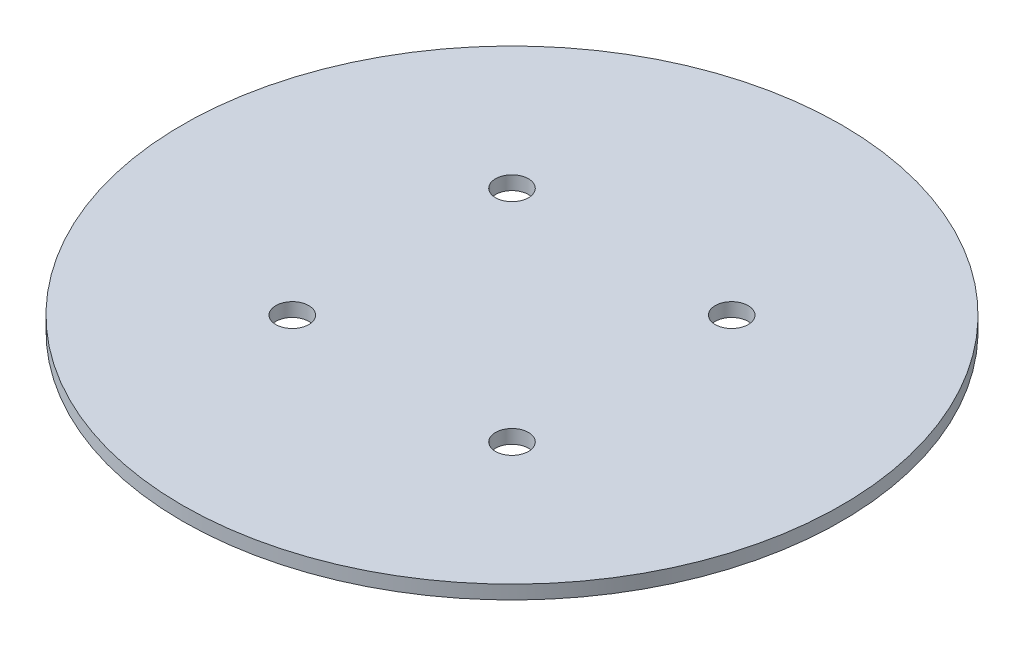
SolidWorks part; units mm, degrees
ref_plane "Front Plane" through (0, 0, 0) normal (0, 0, 1) x (1, 0, 0)
ref_plane "Top Plane" through (0, 0, 0) normal (0, 1, 0) x (1, 0, 0)
ref_plane "Right Plane" through (0, 0, 0) normal (1, 0, 0) x (0, 0, -1)
sketch "Sketch1" plane through (0, 0, 0) normal (0, 1, 0) x (1, 0, 0)
  line L0 (0, 0) -> (-56.8762, 0) construction
  line L1 (0, 19.7977) -> (0, 0) construction
  circle A0 centre (0, 0) radius 76.2
  circle A1 centre (-25.4, 25.4) radius 3.81
  circle A2 centre (-25.4, -25.4) radius 3.81
  circle A3 centre (25.4, -25.4) radius 3.81
  circle A4 centre (25.4, 25.4) radius 3.81
  dimension "D1" = 152.4
  dimension "D2" = 7.62
  dimension "D3" = 25.4
  dimension "D4" = 25.4
extrude "Boss-Extrude1" add sketch "Sketch1" along normal blind 3.175
